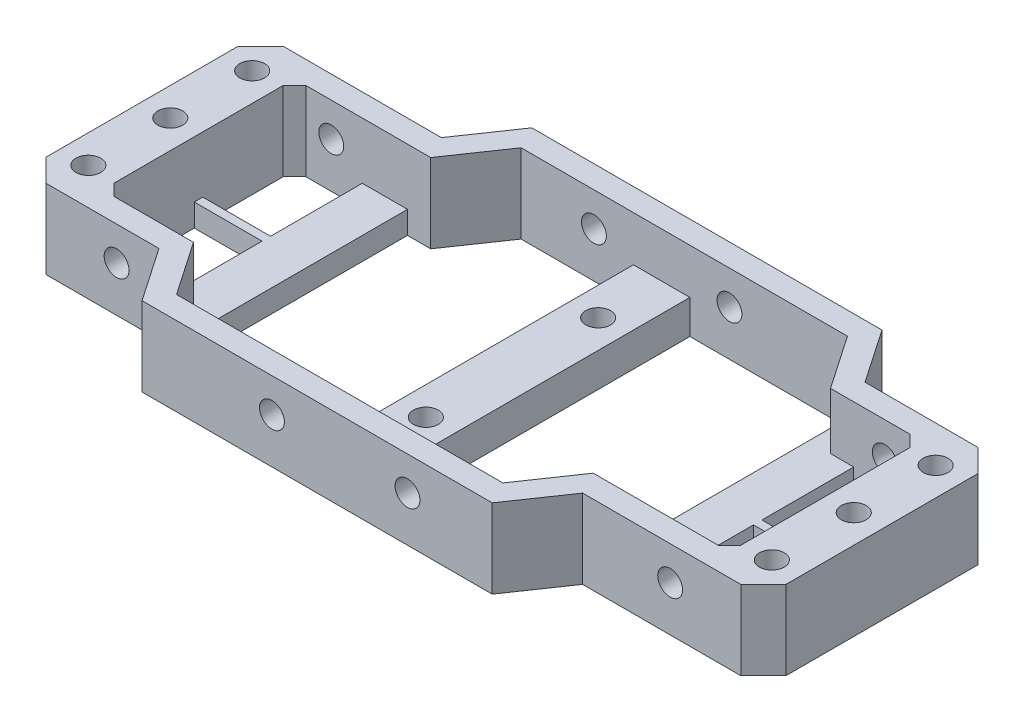
SolidWorks part; units mm, degrees
ref_plane "Front Plane" through (0, 0, 0) normal (0, 0, 1) x (1, 0, 0)
ref_plane "Top Plane" through (0, 0, 0) normal (0, 1, 0) x (1, 0, 0)
ref_plane "Right Plane" through (0, 0, 0) normal (1, 0, 0) x (0, 0, -1)
sketch "Sketch1" plane through (0, 0, 0) normal (0, 1, 0) x (1, 0, 0)
  line L0 (-104.176, 0) -> (26.824, 0) construction
  line L1 (-104.176, -21) -> (-104.176, 21)
  line L2 (26.824, 21) -> (26.824, -21)
  line L3 (-104.176, 21) -> (-72.176, 21)
  line L4 (-94.176, -17) -> (-94.176, 17)
  line L5 (-104.176, -21) -> (-80.176, -21)
  line L6 (26.824, 21) -> (2.824, 21)
  line L7 (26.824, -21) -> (-5.176, -21)
  line L8 (16.824, 17) -> (16.824, -17)
  line L9 (-73.676, -30.5) -> (-11.676, -30.5)
  line L10 (-65.676, 30.5) -> (-3.676, 30.5)
  line L11 (-72.176, 21) -> (-65.676, 30.5)
  line L12 (-3.676, 30.5) -> (2.824, 21)
  line L13 (-80.176, -21) -> (-73.676, -30.5)
  line L14 (-11.676, -30.5) -> (-5.176, -21)
  line L15 (-63.5662, 26.5) -> (-5.7858, 26.5)
  line L16 (-71.5662, -26.5) -> (-13.7858, -26.5)
  line L17 (-94.176, -17) -> (-78.0662, -17)
  line L18 (-71.5662, -26.5) -> (-78.0662, -17)
  line L19 (16.824, -17) -> (-7.2858, -17)
  line L20 (-13.7858, -26.5) -> (-7.2858, -17)
  line L21 (-94.176, 17) -> (-70.0662, 17)
  line L22 (-70.0662, 17) -> (-63.5662, 26.5)
  line L23 (16.824, 17) -> (0.7142, 17)
  line L24 (0.7142, 17) -> (-5.7858, 26.5)
  dimension "D1" = 131
  dimension "D2" = 42
  dimension "D3" = 32
  dimension "D4" = 34
  dimension "D5" = 4
  dimension "D6" = 24
  dimension "D7" = 24
  dimension "D8" = 32
  dimension "D9" = 10
  dimension "D10" = 4
  dimension "D11" = 10
  dimension "D12" = 62
  dimension "D13" = 62
  dimension "D14" = 6.5
  dimension "D15" = 61
  dimension "D16" = 9.5
  dimension "D17" = 6.5
  dimension "D18" = 4
  dimension "D19" = 4
  dimension "D20" = 4
  dimension "D21" = 4
  dimension "D22" = 4
  dimension "D23" = 4
  dimension "D24" = 4
extrude "Boss-Extrude1" add sketch "Sketch1" along normal blind 14
sketch "Sketch2" plane through (0, 0, 0) normal (0, -1, 0) x (-1, 0, 0)
  line L0 (104.176, -21) -> (80.176, -21) construction
  line L1 (72.176, 21) -> (104.176, 21) construction
  line L2 (-26.824, 21) -> (-2.824, 21) construction
  line L3 (5.176, -21) -> (-26.824, -21) construction
  line L4 (104.176, 21) -> (104.176, -21) construction
  line L5 (-26.824, -21) -> (-26.824, 21) construction
  circle A0 centre (99.176, 14.5) radius 2.2
  circle A1 centre (99.176, 0) radius 2.2
  circle A2 centre (99.176, -14.5) radius 2.2
  circle A3 centre (-21.824, -14.5) radius 2.2
  circle A4 centre (-21.824, 0) radius 2.2
  circle A5 centre (-21.824, 14.5) radius 2.2
  dimension "D1" = 4.4
  dimension "D2" = 4.4
  dimension "D3" = 4.4
  dimension "D4" = 4.4
  dimension "D5" = 4.4
  dimension "D6" = 4.4
  dimension "D10" = 6.5
  dimension "D16" = 5
  dimension "D17" = 5
  dimension "D18" = 5
  dimension "D7" = 6.5
  dimension "D8" = 21
  dimension "D9" = 6.5
  dimension "D11" = 21
  dimension "D12" = 6.5
  dimension "D13" = 5
  dimension "D14" = 5
  dimension "D15" = 5
extrude "Cut-Extrude1" cut sketch "Sketch2" against normal up to next
sketch "Sketch5" plane through (0, 0, -30.5) normal (0, 0, -1) x (-1, 0, 0)
  line L0 (104.176, 14) -> (104.176, 0) construction
  line L1 (72.176, 14) -> (104.176, 14) construction
  line L2 (3.676, 14) -> (65.676, 14) construction
  line L3 (-26.824, 14) -> (-2.824, 14) construction
  line L4 (-26.824, 14) -> (-26.824, 0) construction
  circle A0 centre (50.676, 8) radius 2.2
  circle A1 centre (26.676, 8) radius 2.2
  circle A2 centre (87.676, 8) radius 2.2
  circle A3 centre (-10.324, 8) radius 2.2
  dimension "D1" = 4.4
  dimension "D2" = 4.4
  dimension "D3" = 4.4
  dimension "D4" = 4.4
  dimension "D6" = 6
  dimension "D7" = 6
  dimension "D8" = 6
  dimension "D9" = 6
  dimension "D10" = 16.5
  dimension "D11" = 24
  dimension "D5" = 16.5
  dimension "D12" = 53.5
extrude "Cut-Extrude2" cut sketch "Sketch5" against normal through all
sketch "Sketch6" plane through (0, 0, 26.5) normal (0, 0, -1) x (-1, 0, 0)
  line L0 (71.5662, 0) -> (13.7858, 0) construction
  line L1 (43.676, 0) -> (33.676, 0)
  line L2 (43.676, 0) -> (43.676, 6)
  line L3 (43.676, 6) -> (33.676, 6)
  line L4 (33.676, 0) -> (33.676, 6)
  circle A0 centre (50.676, 8) radius 2.2 construction
  dimension "D1" = 10
  dimension "D2" = 7
  dimension "D3" = 6
extrude "Boss-Extrude2" add sketch "Sketch6" along normal up to next
sketch "Sketch7" plane through (0, 0, 0) normal (0, -1, 0) x (1, 0, 0)
  line L0 (-82.176, 17) -> (-82.176, -17)
  line L1 (-94.176, 17) -> (-78.0662, 17) construction
  line L2 (-70.0662, -17) -> (-94.176, -17) construction
  line L3 (-94.176, -17) -> (-94.176, 17) construction
  line L4 (-94.176, 0.75) -> (-82.176, 0.75)
  line L5 (-94.176, -0.75) -> (-82.176, -0.75)
  line L6 (-74.176, 22.6856) -> (-74.176, -17)
  line L7 (-78.0662, 17) -> (-71.5662, 26.5) construction
  line L8 (-82.176, 17) -> (-78.0662, 17)
  line L9 (-78.0662, 17) -> (-74.176, 22.6856)
  line L10 (-82.176, -17) -> (-74.176, -17)
  line L11 (4.824, 17) -> (4.824, -17)
  line L12 (-7.2858, 17) -> (16.824, 17) construction
  line L13 (16.824, -17) -> (0.7142, -17) construction
  line L14 (16.824, 17) -> (16.824, -17) construction
  line L15 (4.824, 0.75) -> (16.824, 0.75)
  line L16 (4.824, -0.75) -> (16.824, -0.75)
  line L17 (-3.176, 17) -> (-3.176, -22.6856)
  line L19 (0.7142, -17) -> (-5.7858, -26.5) construction
  dimension "D1" = 12
  dimension "D2" = 16.25
  dimension "D3" = 16.25
  dimension "D4" = 8
  dimension "D6" = 12
  dimension "D7" = 16.25
  dimension "D8" = 8
extrude "Boss-Extrude3" add sketch "Sketch7" against normal blind 4
sketch "Sketch8" plane through (0, 0, 0) normal (0, -1, 0) x (-1, 0, 0)
  line L0 (73.676, -30.5) -> (11.676, -30.5) construction
  line L1 (3.676, 30.5) -> (65.676, 30.5) construction
  line L2 (43.676, 26.5) -> (43.676, -26.5) construction
  circle A0 centre (38.676, -15.25) radius 2.2
  circle A1 centre (38.676, 15.25) radius 2.2
  dimension "D1" = 4.4
  dimension "D2" = 4.4
  dimension "D3" = 15.25
  dimension "D4" = 15.25
  dimension "D6" = 5
  dimension "D5" = 5
extrude "Cut-Extrude3" cut sketch "Sketch8" against normal up to next
chamfer "Chamfer1" distance 4 angle 45 4 edges at (-104.176, 7, 21) (26.824, 7, 21) (26.824, 7, -21) (-104.176, 7, -21)
chamfer "Chamfer2" distance 2 angle 45 4 edges at (16.824, 7, -17) (16.824, 7, 17) (-94.176, 7, -17) (-94.176, 7, 17)
